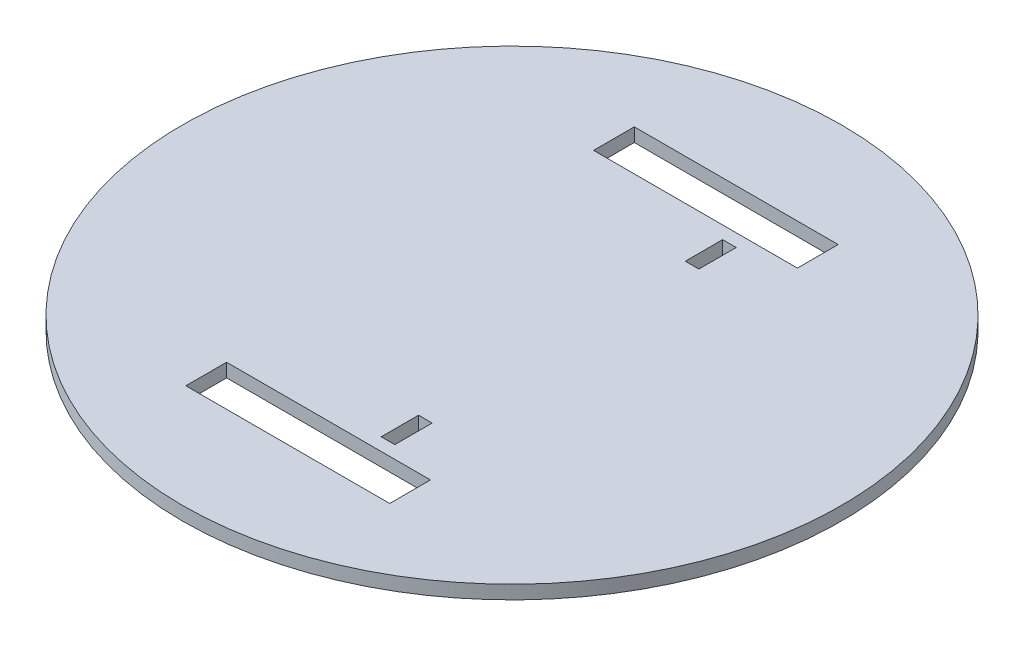
SolidWorks part; units mm, degrees
ref_plane "Спереди" through (0, 0, 0) normal (0, 0, 1) x (1, 0, 0)
ref_plane "Сверху" through (0, 0, 0) normal (0, 1, 0) x (1, 0, 0)
ref_plane "Справа" through (0, 0, 0) normal (1, 0, 0) x (0, 0, -1)
sketch "Sketch1" plane through (0, 0, 0) normal (0, 1, 0) x (1, 0, 0)
  circle A0 centre (0, 0) radius 97
  dimension "D1" = 194
extrude "Boss-Extrude1" add sketch "Sketch1" along normal blind 4
sketch "Sketch2" plane through (0, 4, 0) normal (0, 1, 0) x (1, 0, 0)
  line L0 (0, -97) -> (0, 97) construction
  line L2 (-30, -54) -> (30, -54)
  line L3 (-30, -54) -> (-30, -66)
  line L4 (-30, -66) -> (30, -66)
  line L5 (30, -54) -> (30, -66)
  line L6 (-30, -54) -> (30, -66) construction
  line L7 (-30, -66) -> (30, -54) construction
  line L8 (-30, 66) -> (30, 66)
  line L9 (-30, 66) -> (-30, 54)
  line L10 (-30, 54) -> (30, 54)
  line L11 (30, 66) -> (30, 54)
  line L12 (-30, 66) -> (30, 54) construction
  line L13 (-30, 54) -> (30, 66) construction
  circle A0 centre (0, 0) radius 97 construction
  point P5 (0, -60)
  point P10 (0, 60)
  dimension "D1" = 60
  dimension "D2" = 60
  dimension "D3" = 12
  dimension "D4" = 12
  dimension "D5" = 60
  dimension "D6" = 60
extrude "Cut-Extrude1" cut sketch "Sketch2" against normal blind 10
sketch "Sketch3" plane through (0, 4, 0) normal (0, 1, 0) x (1, 0, 0)
  line L0 (30, -66) -> (30, -54) construction
  line L7 (11.75, -39.25) -> (15.75, -39.25)
  line L8 (11.75, -39.25) -> (11.75, -50.25)
  line L9 (11.75, -50.25) -> (15.75, -50.25)
  line L10 (15.75, -39.25) -> (15.75, -50.25)
  line L11 (11.75, -39.25) -> (15.75, -50.25) construction
  line L12 (11.75, -50.25) -> (15.75, -39.25) construction
  line L14 (-97, 0) -> (97, 0) construction
  line L15 (11.75, 50.25) -> (15.75, 39.25) construction
  line L16 (11.75, 39.25) -> (15.75, 50.25) construction
  line L19 (15.75, 39.25) -> (15.75, 50.25)
  line L20 (11.75, 50.25) -> (15.75, 50.25)
  line L21 (11.75, 39.25) -> (11.75, 50.25)
  line L22 (11.75, 39.25) -> (15.75, 39.25)
  circle A0 centre (0, 0) radius 97 construction
  point P0 (30, -60)
  point P5 (13.75, -44.75)
  point P26 (13.75, 44.75)
  dimension "D1" = 11
  dimension "D2" = 4
  dimension "D3" = 44.75
  dimension "D4" = 16.25
extrude "Cut-Extrude2" cut sketch "Sketch3" against normal blind 10
